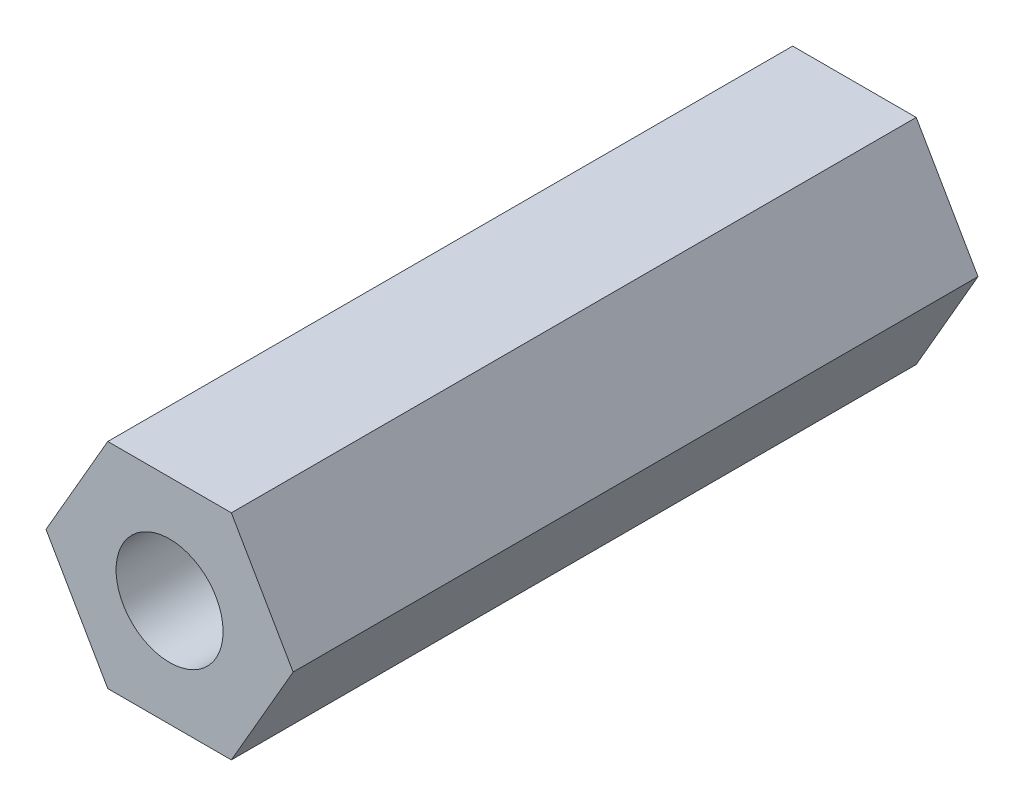
SolidWorks part; units mm, degrees
ref_plane "Front Plane" through (0, 0, 0) normal (0, 0, 1) x (1, 0, 0)
ref_plane "Top Plane" through (0, 0, 0) normal (0, 1, 0) x (1, 0, 0)
ref_plane "Right Plane" through (0, 0, 0) normal (1, 0, 0) x (0, 0, -1)
sketch "Sketch1" plane through (0, 0, 0) normal (0, 0, 1) x (1, 0, 0)
  line L1 (2.8868, 0) -> (1.4434, 2.5)
  line L2 (1.4434, 2.5) -> (-1.4434, 2.5)
  line L3 (-1.4434, 2.5) -> (-2.8868, 0)
  line L4 (-2.8868, 0) -> (-1.4434, -2.5)
  line L5 (-1.4434, -2.5) -> (1.4434, -2.5)
  line L6 (1.4434, -2.5) -> (2.8868, 0)
  circle A0 centre (0, 0) radius 2.5 construction
  circle A1 centre (0, 0) radius 1.25
  dimension "D1" = 2.5
  dimension "D2" = 5
extrude "Boss-Extrude1" add sketch "Sketch1" along normal blind 16
